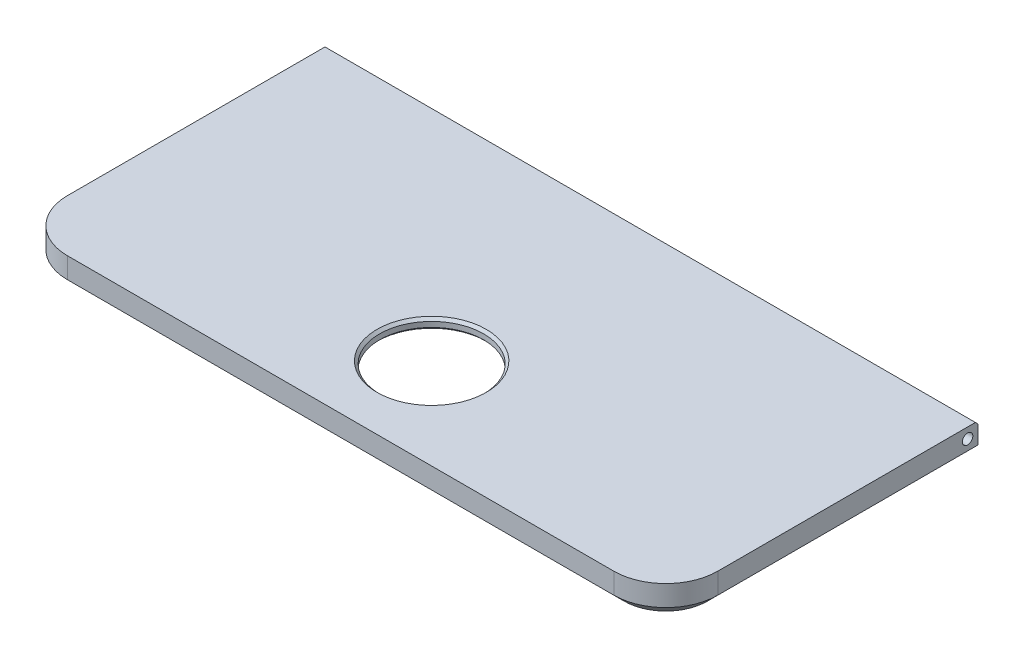
SolidWorks part; units mm, degrees
material "ПК/АБС"
ref_plane "Спереди" through (0, 0, 0) normal (0, 0, 1) x (1, 0, 0)
ref_plane "Сверху" through (0, 0, 0) normal (0, 1, 0) x (1, 0, 0)
ref_plane "Справа" through (0, 0, 0) normal (1, 0, 0) x (0, 0, -1)
sketch "Эскиз1" plane through (0, 0, 0) normal (0, 1, 0) x (1, 0, 0)
  line L1 (-62.5, -30) -> (62.5, -30)
  line L2 (-62.5, -30) -> (-62.5, 30)
  line L3 (-62.5, 30) -> (62.5, 30)
  line L4 (62.5, -30) -> (62.5, 30)
  line L5 (-62.5, -30) -> (62.5, 30) construction
  line L6 (-62.5, 30) -> (62.5, -30) construction
  point P0 (0, 0)
  dimension "D1" = 125
  dimension "D2" = 60
extrude "Бобышка-Вытянуть1" add sketch "Эскиз1" along normal blind 6
fillet "Скругление1" radius 10 2 edges at (-62.5, 3, 30) (62.5, 3, 30)
sketch "Эскиз2" plane through (0, 0, 0) normal (0, -1, 0) x (1, 0, 0)
  line L8 (-59, 20) -> (-59, -26.5)
  line L9 (-59, -26.5) -> (59, -26.5)
  line L10 (59, -26.5) -> (59, 20)
  line L11 (52.5, 26.5) -> (-52.5, 26.5)
  line L12 (-59, 20) -> (-59, -26.5)
  line L13 (-59, -26.5) -> (59, -26.5)
  line L14 (59, -26.5) -> (59, 20)
  line L15 (52.5, 26.5) -> (-52.5, 26.5)
  arc A4 (59, 20) -> (52.5, 26.5) centre (52.5, 20) ccw
  arc A5 (-52.5, 26.5) -> (-59, 20) centre (-52.5, 20) ccw
  arc A6 (59, 20) -> (52.5, 26.5) centre (52.5, 20) ccw
  arc A7 (-52.5, 26.5) -> (-59, 20) centre (-52.5, 20) ccw
  dimension "D1" = 3.5
extrude "Вырез-Вытянуть1" cut sketch "Эскиз2" against normal blind 4
chamfer "Фаска1" distance 2 angle 45 6 edges at (0, 0, -30) (-62.5, 0, -5) (62.5, 0, -5) (-59.5711, 0, 27.0711) (59.5711, 0, 27.0711) (0, 0, 30)
sketch "Эскиз4" plane through (0, 4, 0) normal (0, -1, 0) x (1, 0, 0)
  line L6 (-59, -26.5) -> (59, -26.5)
  line L7 (-59, -26.5) -> (-59, -25)
  line L8 (-59, -25) -> (59, -25)
  line L9 (59, -26.5) -> (59, -25)
  line L14 (62.5, -30) -> (-62.5, -30) construction
  dimension "D2" = 5
extrude "Бобышка-Вытянуть3" add sketch "Эскиз4" along normal up to surface (4 mm away) up to face at (0, 0, 7.219)
sketch "Эскиз3" plane through (62.5, 0, 0) normal (1, 0, 0) x (0, 0, -1)
  line L0 (-20, 6) -> (30, 6) construction
  line L1 (30, 6) -> (30, 2) construction
  circle A0 centre (28, 4) radius 1
  dimension "D2" = 2
  dimension "D1" = 2
  dimension "D3" = 2
extrude "Вырез-Вытянуть2" cut sketch "Эскиз3" against normal blind 10
sketch "Эскиз5" plane through (-62.5, 0, 0) normal (-1, 0, 0) x (0, 0, 1)
  line L0 (-30, 6) -> (-30, 2) construction
  line L1 (-30, 6) -> (20, 6) construction
  circle A0 centre (-28, 4) radius 1
  dimension "D3" = 2
  dimension "D1" = 2
  dimension "D2" = 2
extrude "Вырез-Вытянуть3" cut sketch "Эскиз5" against normal blind 10
sketch "Эскиз6" plane through (0, 4, 0) normal (0, -1, 0) x (1, 0, 0)
  line L0 (0, 30) -> (0, 12.5) construction
  line L1 (-52.5, 30) -> (52.5, 30) construction
  circle A0 centre (0, 12.5) radius 10
  dimension "D2" = 20
  dimension "D1" = 17.5
extrude "Вырез-Вытянуть4" cut sketch "Эскиз6" against normal up to surface (2 mm away) up to face at (0, 6, 7.357)
chamfer "Фаска2" distance 0.5 angle 45 3 edges at (0, 6, -30) (0, 4, 2.5) (0, 6, 2.5)
